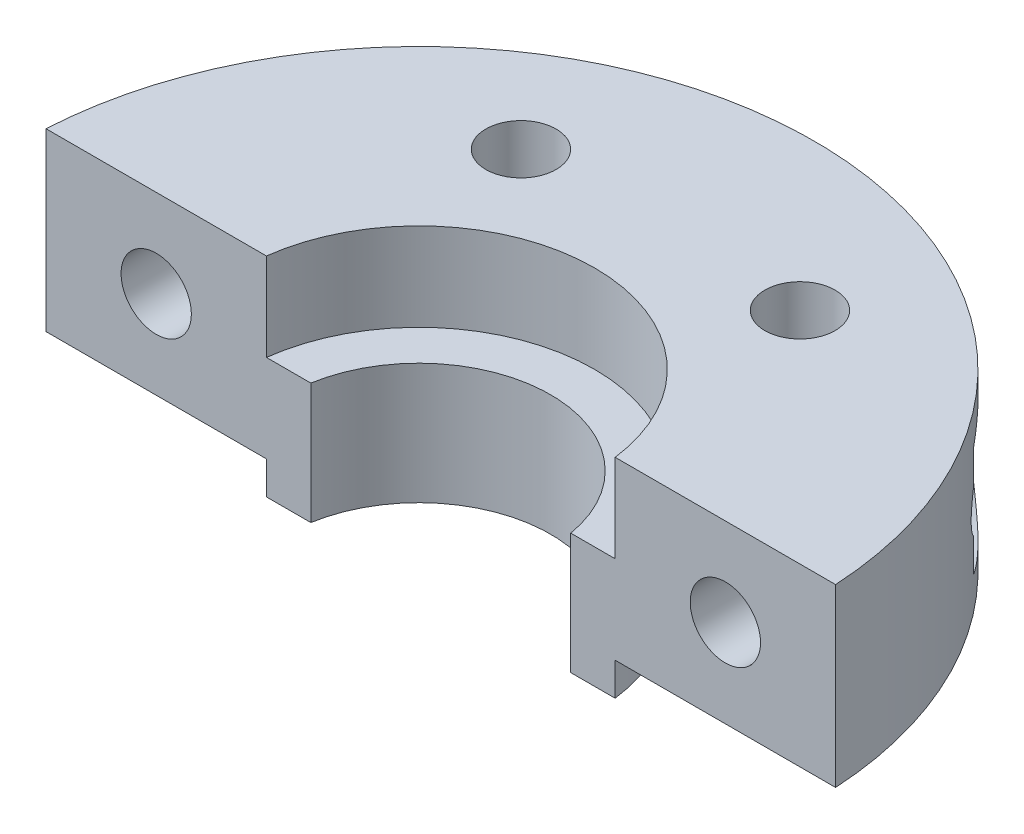
SolidWorks part; units mm, degrees
material "ABS"
ref_plane "Front Plane" through (0, 0, 0) normal (0, 0, 1) x (1, 0, 0)
ref_plane "Top Plane" through (0, 0, 0) normal (0, 1, 0) x (1, 0, 0)
ref_plane "Right Plane" through (0, 0, 0) normal (1, 0, 0) x (0, 0, -1)
sketch "Sketch1" plane through (0, 0, 0) normal (0, 1, 0) x (1, 0, 0)
  line L1 (12.7017, 0) -> (6.3509, 11) construction
  line L2 (6.3509, 11) -> (-6.3509, 11) construction
  line L3 (-6.3509, 11) -> (-12.7017, 0) construction
  line L4 (-12.7017, 0) -> (-6.3509, -11) construction
  line L5 (-6.3509, -11) -> (6.3509, -11) construction
  line L6 (6.3509, -11) -> (12.7017, 0) construction
  circle A0 centre (0, 0) radius 8
  circle A1 centre (0, 0) radius 18
  circle A2 centre (0, 0) radius 11 construction
  circle A3 centre (-6.3509, 11) radius 1.6
  circle A4 centre (6.3509, 11) radius 1.6
  dimension "D1" = 16
  dimension "D2" = 10
  dimension "D3" = 22
  dimension "D4" = 3.2
extrude "Boss-Extrude1" add sketch "Sketch1" along normal blind 8
ref_plane "Plane1" through (0, 4, 0) normal (0, 1, 0) x (1, 0, 0)
sketch "Sketch2" plane through (0, 4, 0) normal (0, 1, 0) x (1, 0, 0)
  circle A0 centre (0, 0) radius 8
  circle A1 centre (0, 0) radius 6
  dimension "D1" = 16
  dimension "D2" = 12
extrude "Boss-Extrude2" add sketch "Sketch2" against normal blind 5.5
sketch "Sketch3" plane through (0, 8, 0) normal (0, 1, 0) x (1, 0, 0)
  line L0 (-20, 1) -> (20, 1)
  line L1 (20, 1) -> (20, -19)
  line L2 (20, -19) -> (-20, -19)
  line L3 (-20, -19) -> (-20, 1)
  line L4 (0, 0) -> (0, 1) construction
  dimension "D1" = 20
  dimension "D2" = 1
  dimension "D3" = 40
extrude "Cut-Extrude1" cut sketch "Sketch3" against normal through all
sketch "Sketch5" plane through (0, 0, -1) normal (0, 0, 1) x (1, 0, 0)
  line L0 (-7.9373, 8) -> (-17.9722, 8) construction
  line L1 (-12.9547, 8) -> (-12.9547, 4) construction
  line L2 (-17.9722, 4) -> (-12.9547, 4) construction
  line L3 (-17.9722, 0) -> (-17.9722, 8) construction
  line L4 (12.9547, 8) -> (12.9547, 4) construction
  line L5 (17.9722, 8) -> (7.9373, 8) construction
  line L6 (12.9547, 4) -> (17.9722, 4) construction
  line L7 (17.9722, 8) -> (17.9722, 0) construction
  circle A0 centre (-12.9547, 4) radius 1.6
  circle A1 centre (12.9547, 4) radius 1.6
  dimension "D1" = 3.2
extrude "Cut-Extrude2" cut sketch "Sketch5" against normal up to next
sketch "Sketch6" plane through (0, 0, -1) normal (0, 0, 1) x (1, 0, 0)
  circle A0 centre (-12.9547, 4) radius 2.8
  circle A1 centre (12.9547, 4) radius 2.8
  dimension "D1" = 5.6
extrude "Cut-Extrude3" cut sketch "Sketch6" against normal up to next from offset 10
